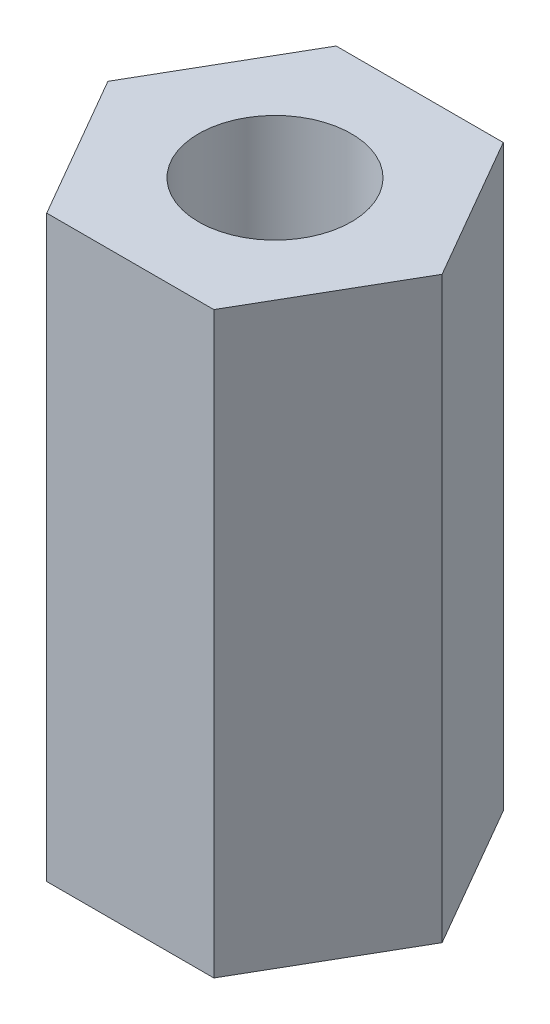
SolidWorks part; units mm, degrees
ref_plane "Front Plane" through (0, 0, 0) normal (0, 0, 1) x (1, 0, 0)
ref_plane "Top Plane" through (0, 0, 0) normal (0, 1, 0) x (1, 0, 0)
ref_plane "Right Plane" through (0, 0, 0) normal (1, 0, 0) x (0, 0, -1)
sketch "Sketch1" plane through (0, 0, 0) normal (0, 1, 0) x (1, 0, 0)
  line L1 (7.3323, 0) -> (3.6662, 6.35)
  line L2 (3.6662, 6.35) -> (-3.6662, 6.35)
  line L3 (-3.6662, 6.35) -> (-7.3323, 0)
  line L4 (-7.3323, 0) -> (-3.6662, -6.35)
  line L5 (-3.6662, -6.35) -> (3.6662, -6.35)
  line L6 (3.6662, -6.35) -> (7.3323, 0)
  circle A0 centre (0, 0) radius 6.35 construction
  circle A1 centre (0, 0) radius 3.3528
  dimension "D2" = 6.7056
  dimension "D1" = 12.7
extrude "Boss-Extrude1" add sketch "Sketch1" along normal blind 25.4
